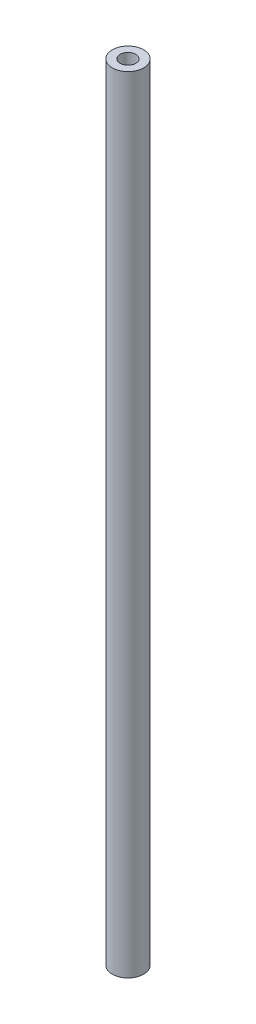
SolidWorks part; units mm, degrees
material "Простая углеродистая сталь"
ref_plane "Спереди" through (0, 0, 0) normal (0, 0, 1) x (1, 0, 0)
ref_plane "Сверху" through (0, 0, 0) normal (0, 1, 0) x (1, 0, 0)
ref_plane "Справа" through (0, 0, 0) normal (1, 0, 0) x (0, 0, -1)
sketch "Эскиз1" plane through (0, 0, 0) normal (0, 1, 0) x (1, 0, 0)
  circle A0 centre (0, 0) radius 1
  circle A1 centre (0, 0) radius 2
  dimension "D1" = 4
  dimension "D2" = 2
extrude "Бобышка-Вытянуть1" add sketch "Эскиз1" along normal blind 100
